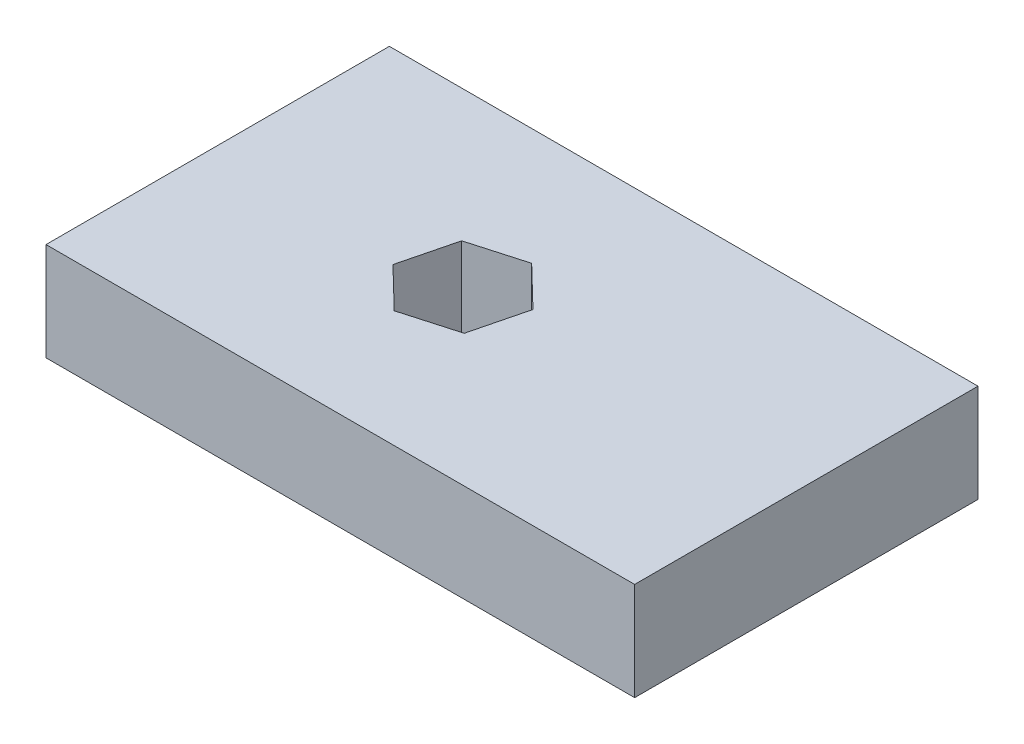
SolidWorks part; units mm, degrees
ref_plane "Front Plane" through (0, 0, 0) normal (0, 0, 1) x (1, 0, 0)
ref_plane "Top Plane" through (0, 0, 0) normal (0, 1, 0) x (1, 0, 0)
ref_plane "Right Plane" through (0, 0, 0) normal (1, 0, 0) x (0, 0, -1)
sketch "Sketch1" plane through (0, 0, 0) normal (0, 1, 0) x (1, 0, 0)
  line L1 (-29.3836, 16.1144) -> (46.8164, 16.1144)
  line L2 (-29.3836, 16.1144) -> (-29.3836, -28.3356)
  line L3 (-29.3836, -28.3356) -> (46.8164, -28.3356)
  line L4 (46.8164, 16.1144) -> (46.8164, -28.3356)
  dimension "D1" = 76.2
  dimension "D2" = 44.45
extrude "Boss-Extrude1" add sketch "Sketch1" along normal blind 12.7
sketch "Sketch2" plane through (0, 12.7, 0) normal (0, 1, 0) x (1, 0, 0)
  line L0 (46.8164, 16.1144) -> (-29.3836, 16.1144) construction
  line L1 (4.1498, 1.0016) -> (-2.9012, -1.01)
  line L2 (-2.9012, -1.01) -> (-4.6846, -8.1222)
  line L3 (-4.6846, -8.1222) -> (0.583, -13.2227)
  line L4 (0.583, -13.2227) -> (7.634, -11.2111)
  line L5 (7.634, -11.2111) -> (9.4174, -4.099)
  line L6 (9.4174, -4.099) -> (4.1498, 1.0016)
  line L7 (-29.3836, 16.1144) -> (-29.3836, -28.3356) construction
  circle A0 centre (2.3664, -6.1106) radius 6.35 construction
  dimension "D1" = 12.7
  dimension "D2" = 22.225
  dimension "D3" = 31.75
extrude "Cut-Extrude1" cut sketch "Sketch2" against normal blind 19.558
